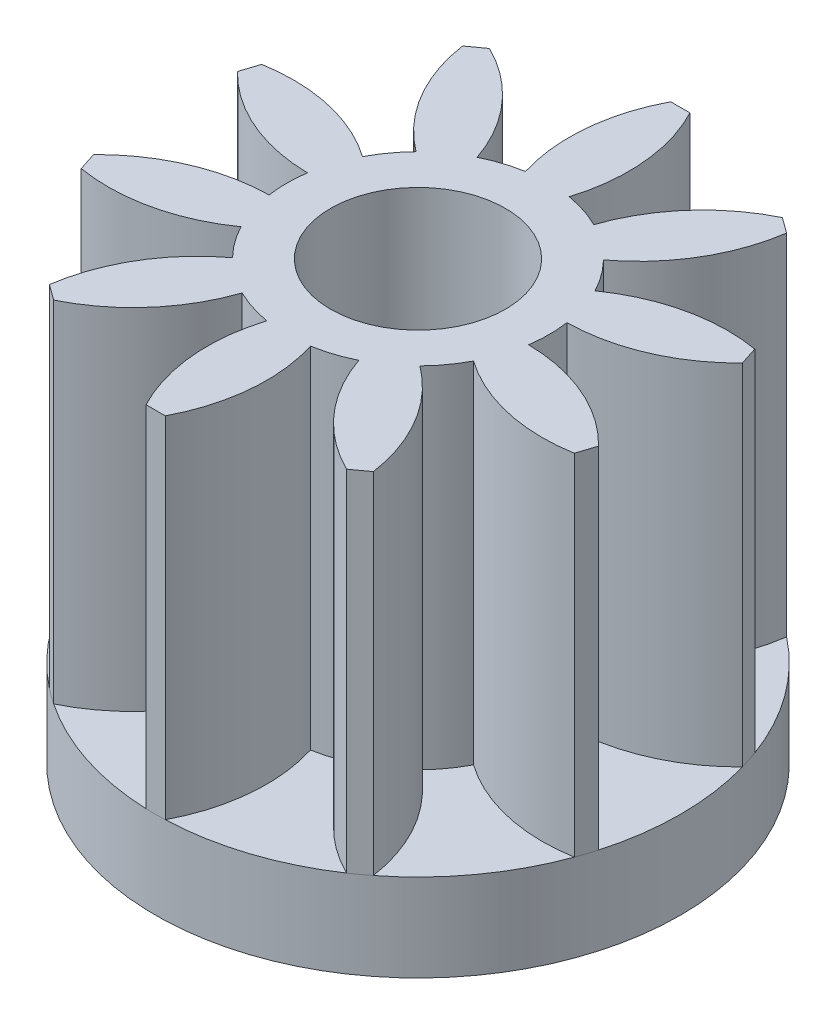
SolidWorks part; units mm, degrees
material "PBT General Purpose"
ref_plane "Front Plane" through (0, 0, 0) normal (0, 0, 1) x (1, 0, 0)
ref_plane "Top Plane" through (0, 0, 0) normal (0, 1, 0) x (1, 0, 0)
ref_plane "Right Plane" through (0, 0, 0) normal (1, 0, 0) x (0, 0, -1)
sketch "Sketch1" plane through (0, 0, 0) normal (0, 1, 0) x (1, 0, 0)
  circle A0 centre (0, 0) radius 1.5
  dimension "D1" = 3
extrude "Boss-Extrude1" add sketch "Sketch1" along normal mid plane 5
sketch "Sketch2" plane through (0, 2.5, 0) normal (0, 1, 0) x (1, 0, 0)
  line L0 (0, 3) -> (0, 0) construction
  line L1 (0, 0) -> (0.25, 1.479) construction
  line L2 (0, 0) -> (-0.25, 1.479) construction
  line L3 (-0.11, 3) -> (0.11, 3)
  circle A0 centre (0, 0) radius 1.5 construction
  arc A1 (-0.25, 1.479) -> (-0.11, 3) centre (1.6607, 2.0701) cw
  arc A2 (0.11, 3) -> (0.25, 1.479) centre (-1.6607, 2.0701) cw
  circle A4 centre (0, 0) radius 1.5
  arc A5 (0.25, 1.479) -> (-0.25, 1.479) centre (0, 0) ccw
  circle M5 centre (0, 0) radius 1.5
  dimension "D1" = 3
  dimension "D5" = 2
  dimension "D3" = 0.5
  dimension "D4" = 0.22
  dimension "D2" = 0
extrude "Boss-Extrude4" add sketch "Sketch2" against normal through all contours A2 L3 A1 M5
pattern_circular "CirPattern1" count 10 over 360 about axis through (0, 0, 0) along (0, 1, 0) of "Boss-Extrude4"
sketch "Sketch3" plane through (0, -2.5, 0) normal (0, -1, 0) x (1, 0, 0)
  circle A0 centre (0, 0) radius 3.002
extrude "Boss-Extrude5" add sketch "Sketch3" against normal blind 1
sketch "Sketch5" plane through (0, -2.5, 0) normal (0, -1, 0) x (1, 0, 0)
  circle A0 centre (0, 0) radius 1
  dimension "D1" = 2
extrude "Cut-Extrude1" cut sketch "Sketch5" against normal through all both and the other way through all
